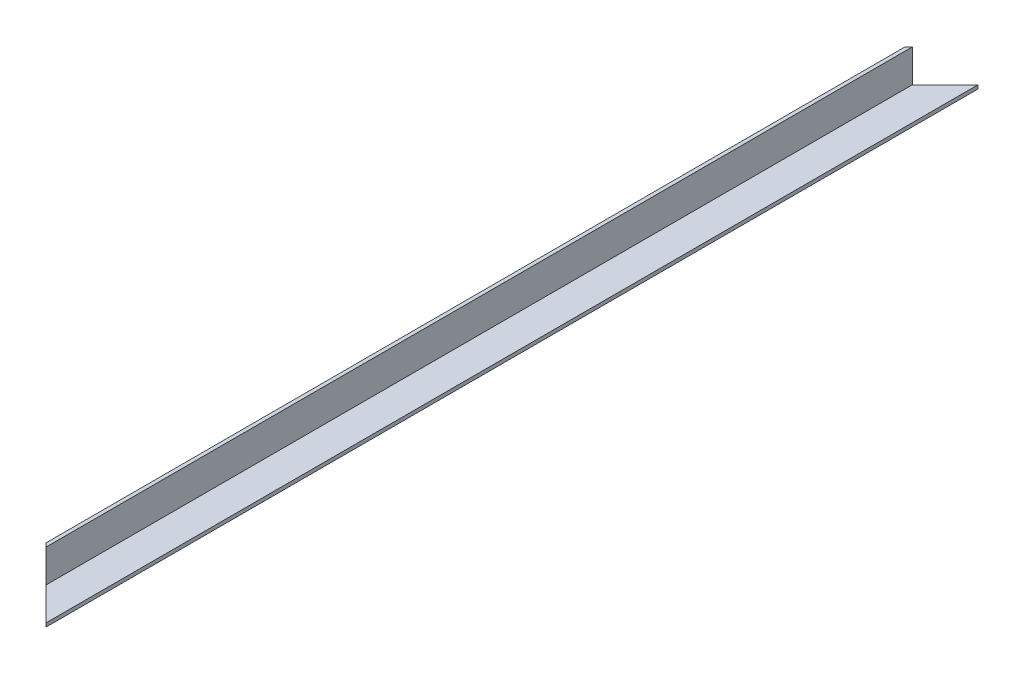
SolidWorks part; units mm, degrees
ref_plane "Front Plane" through (0, 0, 0) normal (0, 0, 1) x (1, 0, 0)
ref_plane "Top Plane" through (0, 0, 0) normal (0, 1, 0) x (1, 0, 0)
ref_plane "Right Plane" through (0, 0, 0) normal (1, 0, 0) x (0, 0, -1)
sketch "Sketch1" plane through (0, 0, 0) normal (0, 0, 1) x (1, 0, 0)
  line L0 (0, 0) -> (20, 0)
  line L4 (2, 20) -> (0, 20)
  line L5 (0, 20) -> (0, 0)
  line L6 (2, 20) -> (2, 2)
  line L7 (2, 2) -> (20, 2)
  line L8 (20, 2) -> (20, 0)
  dimension "D1" = 20
  dimension "D2" = 20
  dimension "D3" = 2
  dimension "D4" = 2
extrude "Boss-Extrude1" add sketch "Sketch1" along normal blind 511
sketch "Sketch2" plane through (0, 2, 0) normal (0, 1, 0) x (1, 0, 0)
  line L0 (0, -511) -> (20, -511)
  line L1 (20, -511) -> (0, -491)
  line L2 (0, -511) -> (0, 0) construction
  line L3 (0, -491) -> (0, -511)
  line L4 (20, 0) -> (0, -20)
  line L5 (0, -20) -> (0, 0)
  line L6 (0, 0) -> (20, 0)
  dimension "D1" = 20
extrude "Cut-Extrude1" cut sketch "Sketch2" along normal mid plane 46
